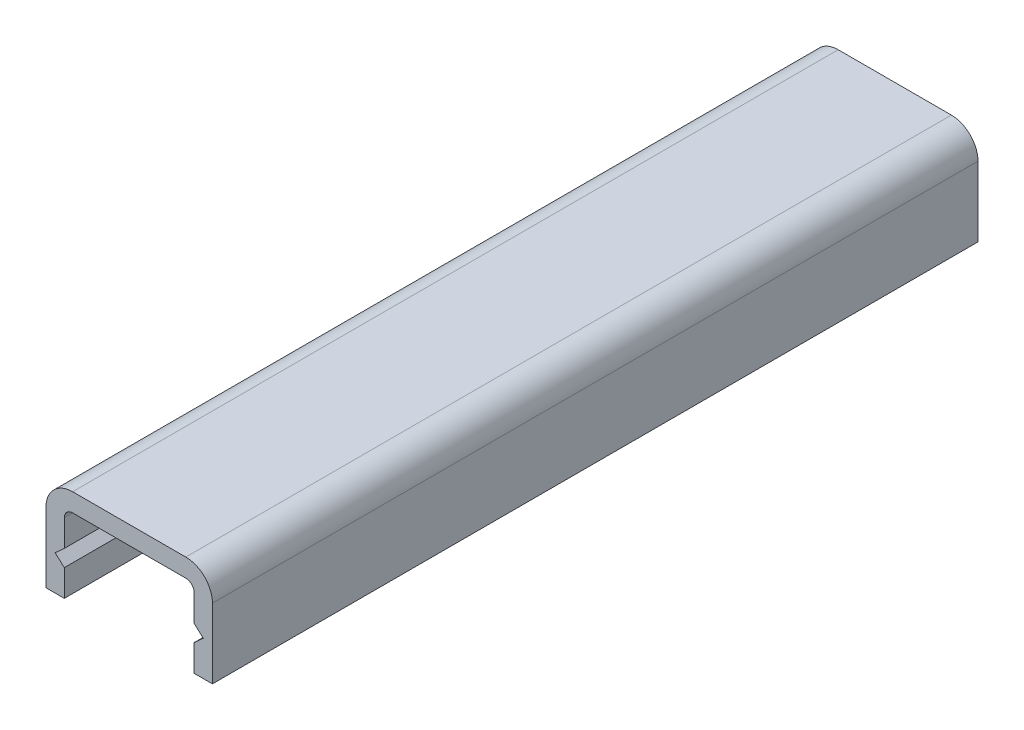
SolidWorks part; units mm, degrees
ref_plane "Plan de face" through (0, 0, 0) normal (0, 0, 1) x (1, 0, 0)
ref_plane "Plan de dessus" through (0, 0, 0) normal (0, 1, 0) x (1, 0, 0)
ref_plane "Plan de droite" through (0, 0, 0) normal (1, 0, 0) x (0, 0, -1)
sketch "Esquisse1" plane through (0, 0, 0) normal (0, 0, 1) x (1, 0, 0)
  line L0 (1.6, 5.8) -> (8.4, 5.8)
  line L1 (10, 4.2) -> (10, 0)
  line L2 (10, 0) -> (8.9, 0)
  line L3 (0, 4.2) -> (0, 0)
  line L4 (1.1, 2.6) -> (8.9, 2.6) construction
  line L5 (8.9, 4.2) -> (8.9, 2.6)
  line L6 (1.6, 4.7) -> (8.4, 4.7)
  line L7 (1.1, 4.2) -> (1.1, 2.6)
  line L8 (0, 0) -> (1.1, 0)
  line L9 (8.9, 4.7) -> (8.9, 1.1) construction
  line L10 (0, 5.8) -> (10, 5.8) construction
  line L11 (0, 5.8) -> (0, 0) construction
  line L12 (1.1, 4.7) -> (8.9, 4.7) construction
  line L13 (1.1, 4.7) -> (1.1, 0) construction
  line L14 (10, 5.8) -> (10, 0) construction
  line L15 (1.1, 1.6) -> (1.1, 0)
  line L16 (1.1, 1.6) -> (0.55, 2.1)
  line L17 (8.9, 1.6) -> (8.9, 0)
  line L18 (1.1, 2.6) -> (0.55, 2.1)
  line L19 (8.9, 2.6) -> (9.45, 2.1)
  line L20 (8.9, 1.6) -> (9.45, 2.1)
  line L21 (8.9, 1.1) -> (8.9, 1.1) construction
  line L22 (0.55, 2.1) -> (9.45, 2.1) construction
  line L23 (8.9, 1.6) -> (1.1, 1.6) construction
  line L24 (0, 0) -> (10, 0) construction
  arc A1 (1.6, 4.7) -> (1.1, 4.2) centre (1.6, 4.2) ccw
  arc A2 (8.9, 4.2) -> (8.4, 4.7) centre (8.4, 4.2) ccw
  arc A3 (8.4, 5.8) -> (10, 4.2) centre (8.4, 4.2) cw
  arc A4 (0, 4.2) -> (1.6, 5.8) centre (1.6, 4.2) cw
  dimension "D2" = 6.8
  dimension "D3" = 1.6
  dimension "D1" = 1.1
  dimension "D4" = 1.6
  dimension "D5" = 0.5
  dimension "D6" = 0.5
  dimension "D7" = 1.6
  dimension "D8" = 4.2
  dimension "D9" = 0.55
  dimension "D10" = 6.8
  dimension "D11" = 0.55
extrude "Extrusion1" add sketch "Esquisse1" along normal blind 46
